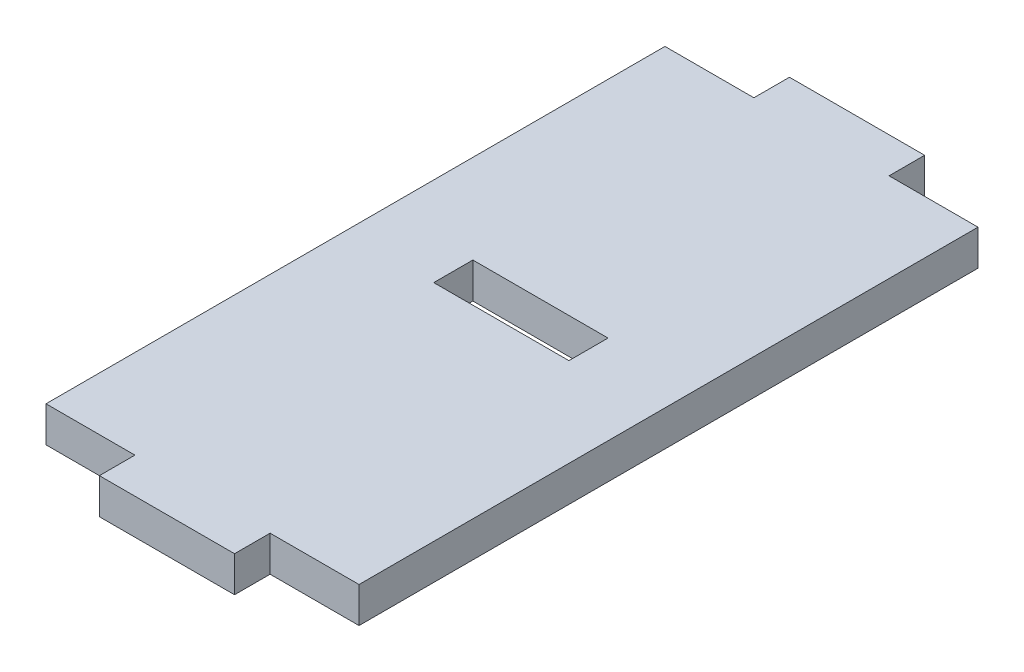
SolidWorks part; units mm, degrees
ref_plane "前视基准面" through (0, 0, 0) normal (0, 0, 1) x (1, 0, 0)
ref_plane "上视基准面" through (0, 0, 0) normal (0, 1, 0) x (1, 0, 0)
ref_plane "右视基准面" through (0, 0, 0) normal (1, 0, 0) x (0, 0, -1)
sketch "草图1" plane through (0, 0, 0) normal (0, 1, 0) x (1, 0, 0)
  line L0 (-2, -2) -> (19.6, -2) construction
  line L1 (0, 0) -> (17.6, 0)
  line L2 (0, 0) -> (0, 34.8)
  line L3 (0, 34.8) -> (17.6, 34.8)
  line L4 (17.6, 0) -> (17.6, 34.8)
  line L5 (19.6, -2) -> (19.6, 36.8) construction
  line L6 (-2, 36.8) -> (19.6, 36.8) construction
  line L7 (-2, -2) -> (-2, 36.8) construction
  line L8 (12.6, 5) -> (12.6, 29.8) construction
  line L9 (5, 29.8) -> (12.6, 29.8) construction
  line L10 (5, 5) -> (5, 29.8) construction
  line L11 (5, 5) -> (12.6, 5) construction
  line L12 (12.6, 5) -> (12.6, -4.6272) construction
  line L13 (5, 5) -> (5, -2) construction
  line L14 (-6.6019, 16.8) -> (28.6178, 16.8) construction
  line L15 (5, 0) -> (12.6, 0)
  line L16 (5, 0) -> (5, -2)
  line L17 (5, -2) -> (12.6, -2)
  line L18 (12.6, 0) -> (12.6, -2)
  line L19 (5, 36.8) -> (12.6, 36.8)
  line L20 (5, 36.8) -> (5, 34.8)
  line L21 (5, 34.8) -> (12.6, 34.8)
  line L22 (12.6, 36.8) -> (12.6, 34.8)
  line L23 (-6.6019, 19) -> (28.6178, 19) construction
  line L24 (-6.6019, 16.8) -> (28.6178, 16.8) construction
  line L25 (5, 19) -> (12.6, 19)
  line L26 (5, 19) -> (5, 16.8)
  line L27 (5, 16.8) -> (12.6, 16.8)
  line L28 (12.6, 19) -> (12.6, 16.8)
  dimension "D1" = 2
  dimension "D2" = 5
  dimension "D3" = 2.2
extrude "凸台-拉伸1" add sketch "草图1" along normal blind 2 contours L1 L4 L3 L2 L25 L28 L27 L26 | L18 L1 L16 L17 | L22 L19 L20 L3
